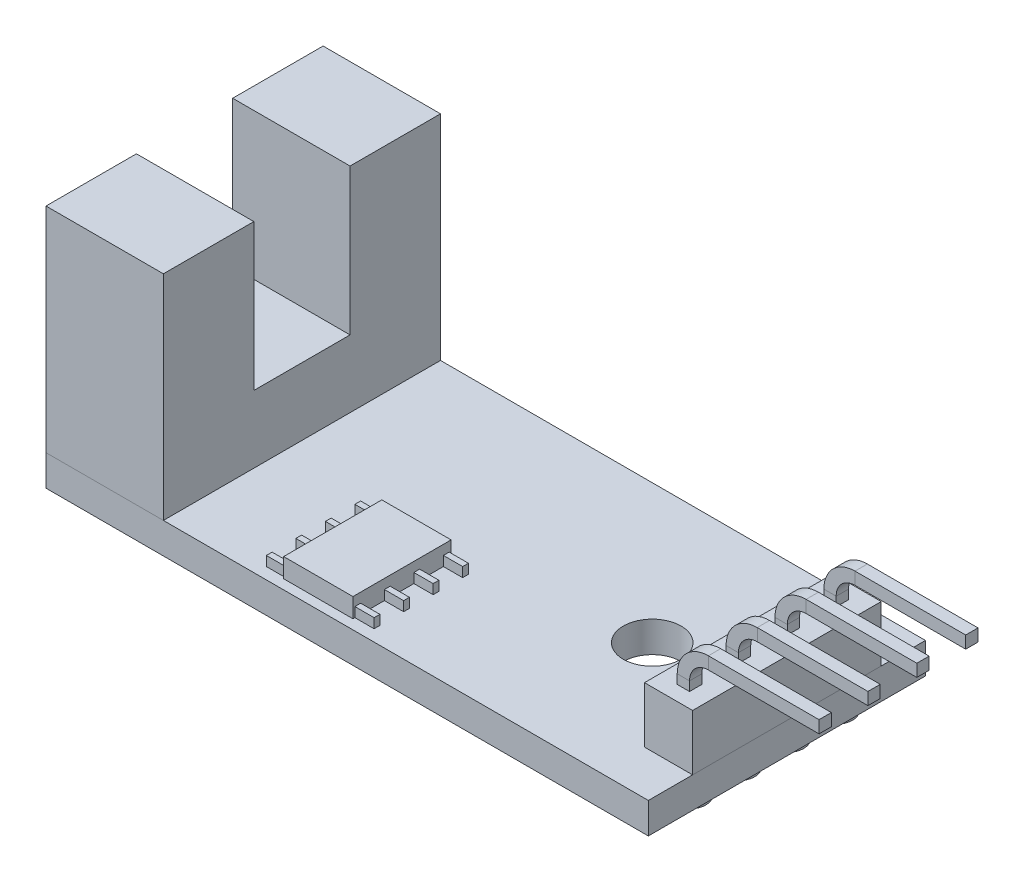
SolidWorks part; units mm, degrees
other "PCB"
other "GND"
other "D0"
other "A0"
other "SENSOR"
other "LM393"
ref_plane "Alzado" through (0, 0, 0) normal (0, 0, 1) x (1, 0, 0)
ref_plane "Planta" through (0, 0, 0) normal (0, 1, 0) x (1, 0, 0)
ref_plane "Vista lateral" through (0, 0, 0) normal (1, 0, 0) x (0, 0, -1)
sketch "Croquis1" plane through (0, 0, 0) normal (0, 1, 0) x (1, 0, 0)
  line L1 (-15.65, -7.2) -> (15.65, -7.2)
  line L2 (-15.65, -7.2) -> (-15.65, 7.2)
  line L3 (-15.65, 7.2) -> (15.65, 7.2)
  line L4 (15.65, -7.2) -> (15.65, 7.2)
  line L5 (-15.65, -7.2) -> (15.65, 7.2) construction
  line L6 (-15.65, 7.2) -> (15.65, -7.2) construction
  circle A0 centre (8.65, 0) radius 1.5
  point P0 (0, 0)
  dimension "D3" = 3
  dimension "D4" = 5.5
  dimension "D1" = 31.3
  dimension "D2" = 14.4
extrude "BASE" add sketch "Croquis1" along normal blind 1.6
sketch "Croquis2" plane through (0, 1.6, 0) normal (0, 1, 0) x (1, 0, 0)
  line L0 (15.65, -7.2) -> (15.65, 7.2) construction
  line L1 (13.15, -4.9) -> (15.65, -4.9)
  line L2 (13.15, -4.9) -> (13.15, 4.9)
  line L3 (13.15, 4.9) -> (15.65, 4.9)
  line L4 (15.65, -4.9) -> (15.65, 4.9)
  line L5 (13.15, -4.9) -> (15.65, 4.9) construction
  line L6 (13.15, 4.9) -> (15.65, -4.9) construction
  line L7 (14.4, 3.81) -> (14.4, 1.27) construction
  line L8 (14.4, 1.27) -> (14.4, -1.27) construction
  line L9 (14.4, -1.27) -> (14.4, -3.81) construction
  point P0 (14.4, 0)
  point P7 (14.4, 3.81)
  point P9 (14.4, 1.27)
  point P10 (14.4, -1.27)
  point P11 (14.4, -3.81)
  point P14 (14.4, 0)
  dimension "D1" = 2.5
  dimension "D2" = 9.8
  dimension "D3" = 2.54
extrude "BASE PINES" add sketch "Croquis2" along normal blind 2.9 separate body
ref_plane "PLANO PIN Vcc" through (0, 0, -3.81) normal (0, 0, 1) x (1, 0, 0)
sketch "DIRECTRIZ" plane through (0, 0, -3.81) normal (0, 0, 1) x (1, 0, 0)
  line L0 (14.4, 4.5) -> (14.4, 4.98)
  line L1 (13.15, 4.5) -> (15.65, 4.5) construction
  line L2 (15.7, 6.28) -> (21.45, 6.28)
  line L3 (13.15, 4.5) -> (13.15, 1.6) construction
  line L4 (21.45, 6.6) -> (21.45, 5.96) construction
  line L5 (-15.65, 0) -> (15.65, 0) construction
  arc A0 (14.4, 4.98) -> (15.7, 6.28) centre (15.7, 4.98) cw
  point P11 (21.45, 6.28)
  dimension "D4" = 1.3
  dimension "D1" = 8.3
  dimension "D2" = 0.64
  dimension "D3" = 6.6
sketch "SECCION" plane through (0, 4.5, 0) normal (0, 1, 0) x (1, 0, 0)
  line L1 (14.08, 4.13) -> (14.72, 4.13)
  line L2 (14.08, 4.13) -> (14.08, 3.49)
  line L3 (14.08, 3.49) -> (14.72, 3.49)
  line L4 (14.72, 4.13) -> (14.72, 3.49)
  line L5 (14.08, 4.13) -> (14.72, 3.49) construction
  line L6 (14.08, 3.49) -> (14.72, 4.13) construction
  point P0 (14.4, 3.81)
  dimension "D1" = 0.64
  dimension "D2" = 0.64
sweep "PIN Vcc" add profiles "SECCION" path "DIRECTRIZ"
pattern_linear "MatrizL1" count 4 spacing 2.54 along (0, 0, 1) of bodies 103
sketch "Croquis5" plane through (0, 1.6, 0) normal (0, 1, 0) x (1, 0, 0)
  line L0 (-15.65, -7.2) -> (15.65, -7.2) construction
  line L1 (-15.65, 7.2) -> (-9.55, 7.2)
  line L2 (-15.65, 7.2) -> (-15.65, -7.2)
  line L3 (-15.65, -7.2) -> (-9.55, -7.2)
  line L4 (-9.55, 7.2) -> (-9.55, -7.2)
  dimension "D1" = 6.1
extrude "CUERPO SENSOR" add sketch "Croquis5" along normal blind 11.1 separate body
sketch "Croquis6" plane through (0, 12.7, 0) normal (0, 1, 0) x (1, 0, 0)
  line L0 (-9.55, -7.2) -> (-9.55, 7.2) construction
  line L1 (-15.65, 2.5) -> (-9.55, 2.5)
  line L2 (-15.65, 2.5) -> (-15.65, -2.5)
  line L3 (-15.65, -2.5) -> (-9.55, -2.5)
  line L4 (-9.55, 2.5) -> (-9.55, -2.5)
  line L5 (-15.65, 2.5) -> (-9.55, -2.5) construction
  line L6 (-15.65, -2.5) -> (-9.55, 2.5) construction
  line L7 (-15.65, 7.2) -> (-15.65, -7.2) construction
  point P0 (-12.6, 0)
  dimension "D1" = 5
extrude "AGUJERO SENSOR" cut sketch "Croquis6" against normal blind 7.6
sketch "Croquis7" plane through (0, 1.6, 0) normal (0, 1, 0) x (1, 0, 0)
  line L0 (-15.65, -7.2) -> (15.65, -7.2) construction
  line L1 (-3.8, -1.6) -> (-0.2, -1.6)
  line L2 (-3.8, -1.6) -> (-3.8, -6.7)
  line L3 (-3.8, -6.7) -> (-0.2, -6.7)
  line L4 (-0.2, -1.6) -> (-0.2, -6.7)
  line L5 (-3.8, -1.6) -> (-0.2, -6.7) construction
  line L6 (-3.8, -6.7) -> (-0.2, -1.6) construction
  point P0 (-2, -4.15)
  dimension "D1" = 2
  dimension "D2" = 0.5
  dimension "D3" = 3.6
  dimension "D4" = 5.1
extrude "Saliente-Extruir4" add sketch "Croquis7" along normal blind 1 separate body
sketch "Croquis8" plane through (0, 1.6, 0) normal (0, 1, 0) x (1, 0, 0)
  line L0 (-3.8, -1.6) -> (-3.8, -6.7) construction
  line L1 (-4.8, -1.7) -> (-3.8, -1.7)
  line L2 (-4.8, -1.7) -> (-4.8, -2)
  line L3 (-4.8, -2) -> (-3.8, -2)
  line L4 (-3.8, -1.7) -> (-3.8, -2)
  line L5 (-0.2, -6.7) -> (-0.2, -1.6) construction
  line L6 (-4.8, -3.2333) -> (-3.8, -3.2333)
  line L7 (-4.8, -3.2333) -> (-4.8, -3.5333)
  line L8 (-4.8, -3.5333) -> (-3.8, -3.5333)
  line L9 (-3.8, -3.2333) -> (-3.8, -3.5333)
  line L10 (-4.8, -4.7667) -> (-3.8, -4.7667)
  line L11 (-4.8, -4.7667) -> (-4.8, -5.0667)
  line L12 (-4.8, -5.0667) -> (-3.8, -5.0667)
  line L13 (-3.8, -4.7667) -> (-3.8, -5.0667)
  line L14 (-4.8, -6.3) -> (-3.8, -6.3)
  line L15 (-4.8, -6.3) -> (-4.8, -6.6)
  line L16 (-4.8, -6.6) -> (-3.8, -6.6)
  line L17 (-3.8, -6.3) -> (-3.8, -6.6)
  line L18 (0.8, -1.7) -> (-0.2, -1.7)
  line L19 (0.8, -1.7) -> (0.8, -2)
  line L20 (0.8, -2) -> (-0.2, -2)
  line L21 (-0.2, -1.7) -> (-0.2, -2)
  line L22 (-0.2, -1.6) -> (-3.8, -1.6) construction
  line L23 (0.8, -3.2333) -> (-0.2, -3.2333)
  line L24 (0.8, -3.2333) -> (0.8, -3.5333)
  line L25 (0.8, -3.5333) -> (-0.2, -3.5333)
  line L26 (-0.2, -3.2333) -> (-0.2, -3.5333)
  line L27 (0.8, -4.7667) -> (-0.2, -4.7667)
  line L28 (0.8, -4.7667) -> (0.8, -5.0667)
  line L29 (0.8, -5.0667) -> (-0.2, -5.0667)
  line L30 (-0.2, -4.7667) -> (-0.2, -5.0667)
  line L31 (0.8, -6.3) -> (-0.2, -6.3)
  line L32 (0.8, -6.3) -> (0.8, -6.6)
  line L33 (0.8, -6.6) -> (-0.2, -6.6)
  line L34 (-0.2, -6.3) -> (-0.2, -6.6)
  line L35 (-4.8, -2) -> (-4.8, -3.2333) construction
  line L36 (-4.8, -3.5333) -> (-4.8, -4.7667) construction
  line L37 (-4.8, -5.0667) -> (-4.8, -6.3) construction
  line L38 (-3.8, -6.7) -> (-0.2, -6.7) construction
  dimension "D1" = 0.1
  dimension "D2" = 0.3
  dimension "D3" = 1
  dimension "D4" = 0.1
extrude "Saliente-Extruir5" add sketch "Croquis8" along normal blind 0.5
sketch "Croquis9" plane through (0, 0, 0) normal (0, -1, 0) x (1, 0, 0)
  line L0 (-10.575, 5.15) -> (-13.15, 5.15) construction
  line L1 (-13.15, 5.15) -> (-13.15, 2.575) construction
  line L2 (-13.15, 2.575) -> (-13.15, 0) construction
  line L3 (-13.15, 0) -> (-13.15, -2.575) construction
  line L4 (-13.15, -2.575) -> (-13.15, -5.15) construction
  line L5 (-13.15, -5.15) -> (-10.575, -5.15) construction
  line L6 (-10.575, -5.15) -> (-10.575, -2.575) construction
  line L7 (-10.575, 5.15) -> (-10.575, 2.575) construction
  line L8 (-15.65, -7.2) -> (-15.65, 7.2) construction
  circle A0 centre (-13.15, 5.15) radius 0.85
  circle A1 centre (-10.575, 5.15) radius 0.85
  circle A2 centre (-10.575, 2.575) radius 0.85
  circle A3 centre (-13.15, 2.575) radius 0.85
  circle A4 centre (-13.15, 0) radius 0.85
  circle A5 centre (-13.15, -2.575) radius 0.85
  circle A6 centre (-13.15, -5.15) radius 0.85
  circle A7 centre (-10.575, -5.15) radius 0.85
  circle A8 centre (-10.575, -2.575) radius 0.85
  circle A9 centre (14.4, 3.81) radius 0.85
  circle A10 centre (14.4, 1.27) radius 0.85
  circle A11 centre (14.4, -1.27) radius 0.85
  circle A12 centre (14.4, -3.81) radius 0.85
  dimension "D1" = 1.7
  dimension "D2" = 12
  dimension "D3" = 2.5
extrude "Saliente-Extruir6" add sketch "Croquis9" along normal blind 0.5
